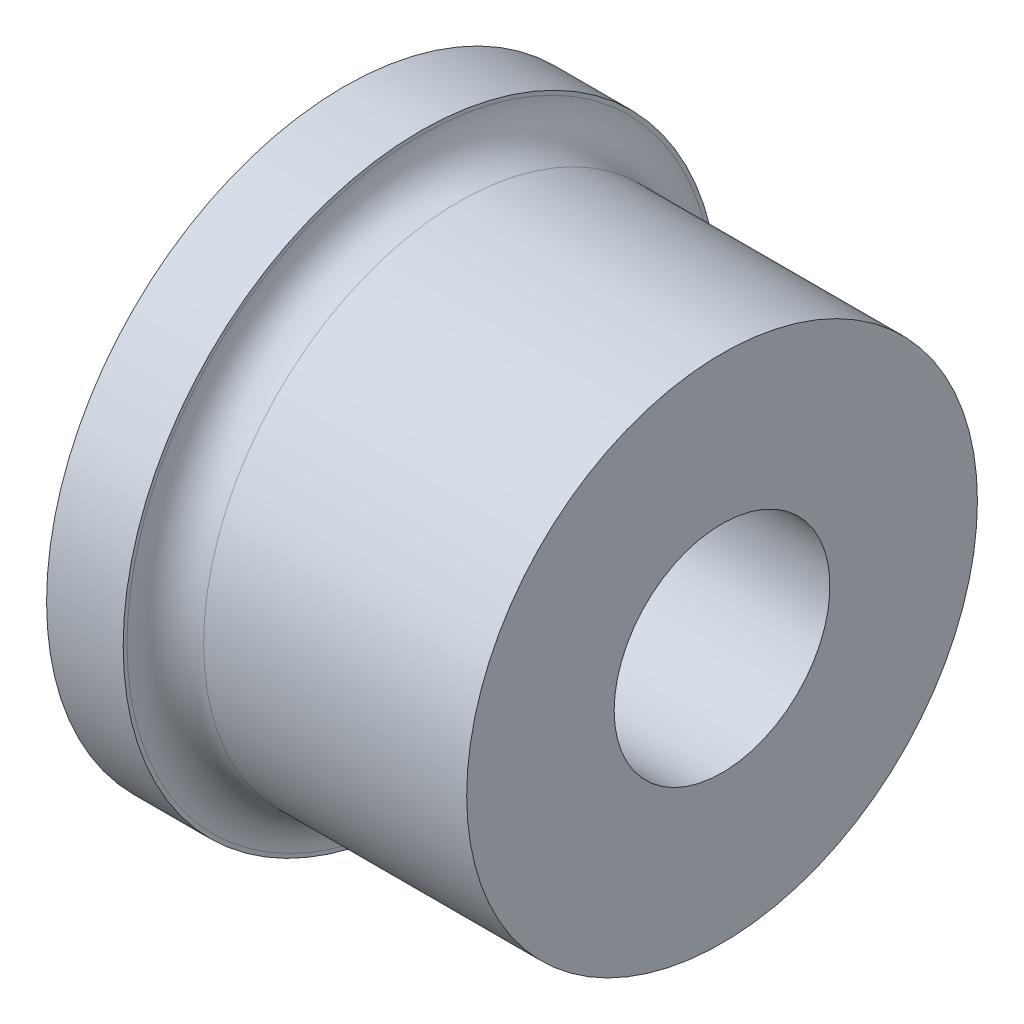
SolidWorks part; units mm, degrees
ref_plane "Front Plane" through (0, 0, 0) normal (0, 0, 1) x (1, 0, 0)
ref_plane "Top Plane" through (0, 0, 0) normal (0, 1, 0) x (1, 0, 0)
ref_plane "Right Plane" through (0, 0, 0) normal (1, 0, 0) x (0, 0, -1)
sketch "Sketch1" plane through (0, 0, 0) normal (0, 1, 0) x (1, 0, 0)
  line L1 (-74.8676, 36) -> (-74.8676, 0) construction
  line L2 (0, 10) -> (0, 0) construction
  line L5 (-74.8676, 0) -> (0, 0) construction
  line L6 (-14.8, 11.65) -> (-14.8, 3.15)
  line L7 (0, 10) -> (0, 4.225)
  line L8 (0, 4.225) -> (-9.8, 4.225)
  line L13 (-9.8, 0.7937) -> (-9.8, 4.225)
  line L16 (0, 10) -> (-10.3, 10)
  line L18 (-16.3, 1.65) -> (-20.8, 1.65)
  line L19 (-20.8, 1.65) -> (-21.8, 1.0937)
  line L20 (-21.8, 1.0937) -> (-21.8, 0.7937)
  line L21 (-21.8, 0.7937) -> (-9.8, 0.7937)
  line L22 (-11.8, 11.5) -> (-11.8, 11.65)
  line L23 (-11.8, 11.65) -> (-14.8, 11.65)
  arc A0 (-14.8, 3.15) -> (-16.3, 1.65) centre (-16.3, 3.15) cw
  arc A1 (-10.3, 10) -> (-11.8, 11.5) centre (-10.3, 11.5) cw
  point P2 (-14.5177, 11.8474)
  point P3 (-15.6993, 15.1671)
  point P6 (-11.8128, 0.7387)
  point P8 (-15.6993, 10.2907)
  point P9 (-21.2023, 1.907)
  point P16 (0, 0)
  point P21 (-22.6822, 1.2839)
  point P23 (-24.0469, 1.0937)
  point P24 (-22.9844, 1.65)
  point P25 (-25.5865, 1.65)
  point P26 (-11.781, 0.7937)
  point P27 (-9.8, 0.7937)
  point P28 (-9.1547, 8.3163)
  point P29 (-8, 8.3892)
  point P30 (0, 8)
  point P31 (-0.2068, 8)
  point P33 (-14.8, 1.65)
  point P36 (-9.9892, 9.8484)
  dimension "D10" = 1.5
  dimension "D12" = 5
  dimension "D2" = 3
  dimension "D3" = 7
  dimension "D4" = 1.65
  dimension "D5" = 0.7937
  dimension "D6" = 4.225
  dimension "D7" = 9.8
  dimension "D8" = 10
  dimension "D9" = 0.3
  dimension "D11" = 1
  dimension "D13" = 10
revolve "Revolve1" add sketch "Sketch1" angle 360 about L5
